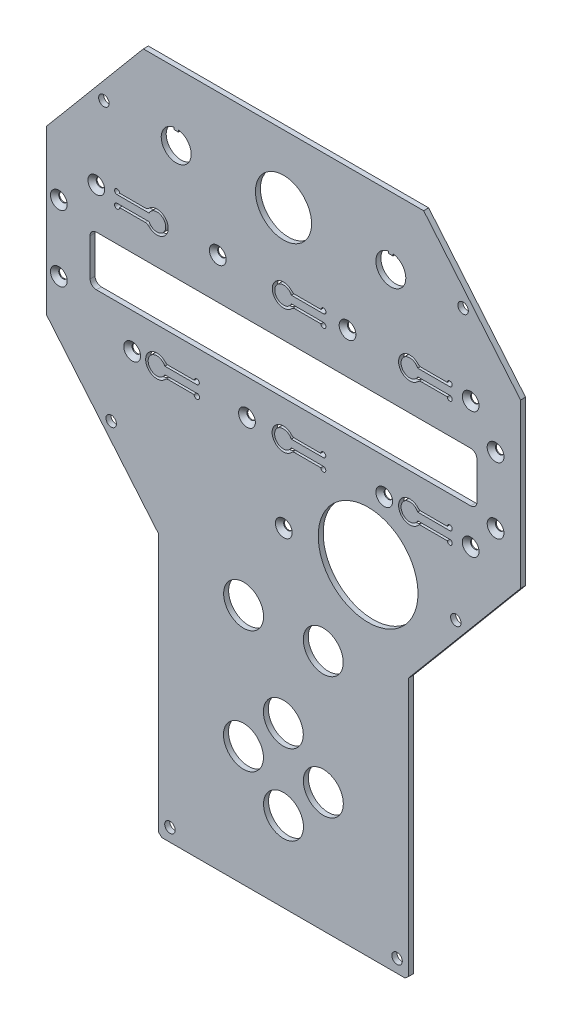
SolidWorks part; units mm, degrees
ref_plane "Plano frontal" through (0, 0, 0) normal (0, 0, 1) x (1, 0, 0)
ref_plane "Plano superior" through (0, 0, 0) normal (0, 1, 0) x (1, 0, 0)
ref_plane "Plano direito" through (0, 0, 0) normal (1, 0, 0) x (0, 0, -1)
sketch "Esboço1" plane through (0, 0, 0) normal (0, 0, 1) x (1, 0, 0)
  line L6 (55.321, 133.8096) -> (-57.007, 133.8096)
  line L7 (-57.007, 133.8096) -> (-95.843, 87.5267)
  line L8 (-95.843, 87.5267) -> (-95.843, 22.1402)
  line L9 (-95.843, 22.1402) -> (-50.843, -31.4887)
  line L10 (-50.843, -31.4887) -> (-50.843, -135.0827)
  line L11 (-50.843, -135.0827) -> (-49.5229, -136.1904)
  line L12 (-49.5229, -136.1904) -> (47.8369, -136.1904)
  line L13 (49.157, -135.0827) -> (47.8369, -136.1904)
  line L14 (49.157, -31.4887) -> (49.157, -135.0827)
  line L15 (94.157, 22.1402) -> (49.157, -31.4887)
  line L16 (94.157, 87.5267) -> (94.157, 22.1402)
  line L17 (55.321, 133.8096) -> (94.157, 87.5267)
  point P16 (-0.843, -136.1904)
  point P17 (-0.843, 133.8096)
extrude "Ressalto-extrusão1" add sketch "Esboço1" along normal blind 2
sketch "Esboço2" plane through (0, 0, 2) normal (0, 0, 1) x (1, 0, 0)
  line L0 (-0.843, -146.6722) -> (-0.843, 180.0647) construction
  line L1 (-95.843, 87.5267) -> (-95.843, 22.1402) construction
  line L2 (55.321, 133.8096) -> (-57.007, 133.8096) construction
  line L3 (-95.843, 22.1402) -> (-50.843, -31.4887) construction
  line L6 (49.157, -135.0827) -> (49.157, -31.4887) construction
  line L7 (-49.5229, -136.1904) -> (47.8369, -136.1904) construction
  line L9 (-50.843, -31.4887) -> (-50.843, -135.0827) construction
  circle A0 centre (-72.8144, 107.9499) radius 2.1
  circle A1 centre (-46.343, -130.9644) radius 2.1
  circle A2 centre (44.657, -130.9644) radius 2.1
  circle A3 centre (71.1284, 107.9499) radius 2.1
  circle A4 centre (-69.8958, -1.7817) radius 2.1
  circle A5 centre (68.2098, -1.7817) radius 2.1
  dimension "D1" = 23.0286
  dimension "D2" = 4.5
  dimension "D3" = 4.5
  dimension "D7" = 25.8597
  dimension "D4" = 5.226
  dimension "D11" = 4.5
extrude "Corte-extrusão1" cut sketch "Esboço2" against normal up to next
sketch "Esboço3" plane through (0, 0, 2) normal (0, 0, 1) x (1, 0, 0)
  line L0 (-95.843, 87.5267) -> (-95.843, 22.1402) construction
  line L1 (-49.5229, -136.1904) -> (47.8369, -136.1904) construction
  line L2 (-75.843, 40.8096) -> (74.157, 40.8096)
  line L3 (-78.343, 43.3096) -> (-78.343, 58.3096)
  line L4 (-75.843, 60.8096) -> (74.157, 60.8096)
  line L5 (76.657, 43.3096) -> (76.657, 58.3096)
  line L6 (-78.343, 40.8096) -> (76.657, 60.8096) construction
  line L7 (-78.343, 60.8096) -> (76.657, 40.8096) construction
  arc A0 (74.157, 60.8096) -> (76.657, 58.3096) centre (74.157, 58.3096) cw
  arc A1 (74.157, 40.8096) -> (76.657, 43.3096) centre (74.157, 43.3096) ccw
  arc A2 (-75.843, 40.8096) -> (-78.343, 43.3096) centre (-75.843, 43.3096) cw
  arc A3 (-78.343, 58.3096) -> (-75.843, 60.8096) centre (-75.843, 58.3096) cw
  dimension "D1" = 2.5
  dimension "D2" = 155
  dimension "D3" = 20
  dimension "D4" = 17.5
  dimension "D5" = 177
extrude "Corte-extrusão2" cut sketch "Esboço3" against normal up to next
sketch "Esboço4" plane through (0, 0, 2) normal (0, 0, 1) x (1, 0, 0)
  line L2 (-49.5229, -136.1904) -> (47.8369, -136.1904) construction
  line L3 (94.157, 22.1402) -> (94.157, 87.5267) construction
  circle A0 centre (33.0563, -0.1904) radius 20
  dimension "D1" = 136
  dimension "D2" = 61.1007
extrude "Corte-extrusão3" cut sketch "Esboço4" against normal up to next
sketch "Esboço5" plane through (0, 0, 2) normal (0, 0, 1) x (1, 0, 0)
  line L2 (55.321, 133.8096) -> (-57.007, 133.8096) construction
  line L3 (-44.743, 112.7417) -> (-44.743, 111.9417)
  line L4 (-44.743, 111.9417) -> (-42.943, 111.9417)
  line L5 (-42.943, 111.9417) -> (-42.943, 112.7417)
  line L6 (41.257, 112.7417) -> (41.257, 111.9417)
  line L7 (41.257, 111.9417) -> (43.057, 111.9417)
  line L8 (43.057, 111.9417) -> (43.057, 112.7417)
  circle A0 centre (-16.8949, -88.1059) radius 8
  circle A1 centre (15.1229, -88.1059) radius 8
  circle A2 centre (-0.843, -104.1412) radius 8
  circle A3 centre (-0.9097, -72.1234) radius 8
  circle A4 centre (-16.8357, -39.1393) radius 8
  circle A5 centre (15.0819, -39.1108) radius 8
  circle A6 centre (-0.843, 106.8096) radius 11.25
  arc A7 (-44.743, 112.7417) -> (-42.943, 112.7417) centre (-43.843, 106.8096) ccw
  arc A8 (41.257, 112.7417) -> (43.057, 112.7417) centre (42.157, 106.8096) ccw
  dimension "D11" = 27
  dimension "D12" = 43
  dimension "D13" = 43
  dimension "D14" = 22.5
  dimension "D15" = 12
  dimension "D16" = 12
  dimension "D18" = 1.8
  dimension "D19" = 0.9
  dimension "D20" = 0.8
  dimension "D21" = 1.8
  dimension "D22" = 0.9
  dimension "D23" = 0.8
extrude "Corte-extrusão4" cut sketch "Esboço5" against normal up to next
sketch "Esboço10" plane through (0, 0, 2) normal (0, 0, 1) x (1, 0, 0)
  line L3 (94.157, 22.1402) -> (94.157, 87.5267) construction
  line L4 (74.157, 60.8096) -> (-75.843, 60.8096) construction
  circle A0 centre (-61.4827, 26.6206) radius 1.75
  circle A1 centre (-15.4827, 26.6206) radius 1.75
  circle A2 centre (39.5173, 26.6206) radius 1.75
  circle A3 centre (84.131, 37.971) radius 1.6
  circle A4 centre (84.131, 64.471) radius 1.6
  circle A5 centre (-90.869, 64.471) radius 1.6
  circle A6 centre (-90.869, 37.971) radius 1.6
  circle A7 centre (-27.183, 77.1996) radius 1.75
  circle A8 centre (24.817, 77.1996) radius 1.75
  circle A9 centre (-0.7327, -4.3294) radius 2
  dimension "D1" = 69.3401
  dimension "D2" = 16.39
  dimension "D3" = 52
  dimension "D4" = 30.95
  dimension "D5" = 14.75
hole_wizard "Escareado para parafuso Allen sextavado escareado de M32" positions "3DSketch3" profile "Esboço11" countersink size "M3" standard "ISO" end condition through all
sketch3d "3DSketch3"
  point P0 (-90.869, 64.471, 2)
  point P3 (-90.869, 37.971, 2)
  point P6 (-61.4827, 26.6206, 2)
  point P9 (-15.4827, 26.6206, 2)
  point P12 (39.5173, 26.6206, 2)
  point P15 (84.131, 37.971, 2)
  point P18 (84.131, 64.471, 2)
  point P21 (24.817, 77.1996, 2)
  point P24 (-27.183, 77.1996, 2)
  point P32 (-0.7327, -4.3294, 2)
sketch "Esboço11" plane through (-90.869, 64.471, 2) normal (1, 0, 0) x (0, -1, 0)
  line L0 (0, 0) -> (0, 2)
  line L1 (0, 2) -> (1.7, 2)
  line L2 (1.7, 2) -> (1.7, 1.66)
  line L3 (1.7, 1.66) -> (3.36, 0)
  line L5 (3.36, 0) -> (0, 0)
  line L6 (-1.7, 1.66) -> (-3.36, 0) construction
  line L11 (0, -6.35) -> (0, 107.95) construction
  dimension "Thru Hole Dia." = 3.4
  dimension "Thru Hole Depth" = 2
  dimension "Near C'Sink Dia." = 6.72
  dimension "Near C'Sink Angle" = 90
sketch "Esboço12" plane through (0, 0, 2) normal (0, 0, 1) x (1, 0, 0)
  line L0 (-75.843, 40.8096) -> (74.157, 40.8096) construction
  line L1 (74.157, 60.8096) -> (-75.843, 60.8096) construction
  line L2 (94.157, 22.1402) -> (94.157, 87.5267) construction
  line L3 (52.9293, 28.0196) -> (65.767, 28.0196)
  line L5 (64.767, 29.0196) -> (53.5087, 29.0196)
  line L6 (52.9293, 25.0196) -> (65.767, 25.0196)
  line L7 (2.2593, 28.0196) -> (15.097, 28.0196)
  line L8 (64.767, 24.0196) -> (53.5087, 24.0196)
  line L9 (14.097, 24.0196) -> (2.8387, 24.0196)
  line L10 (14.097, 29.0196) -> (2.8387, 29.0196)
  line L11 (2.2593, 25.0196) -> (15.097, 25.0196)
  line L12 (-48.4107, 28.0196) -> (-35.573, 28.0196)
  line L13 (-36.6534, 24.0196) -> (-47.8313, 24.0196)
  line L14 (-36.573, 29.0196) -> (-47.8313, 29.0196)
  line L15 (-48.4107, 25.0196) -> (-35.9821, 25.0196)
  line L25 (2.3293, 77.9796) -> (15.167, 77.9796)
  line L26 (52.9293, 77.9796) -> (65.767, 77.9796)
  line L27 (14.167, 78.9796) -> (2.9087, 78.9796)
  line L28 (2.3293, 74.9796) -> (15.167, 74.9796)
  line L29 (-54.6953, 77.9796) -> (-67.533, 77.9796)
  line L30 (14.167, 73.9796) -> (2.9087, 73.9796)
  line L31 (64.767, 78.9796) -> (53.5087, 78.9796)
  line L32 (52.9293, 74.9796) -> (65.767, 74.9796)
  line L34 (64.767, 73.9796) -> (53.5087, 73.9796)
  line L35 (-66.533, 78.9796) -> (-55.2746, 78.9796)
  line L36 (-54.6953, 74.9796) -> (-67.533, 74.9796)
  line L38 (-66.533, 73.9796) -> (-55.2746, 73.9796)
  arc A0 (53.5087, 29.0196) -> (53.5087, 24.0196) centre (49.767, 26.5196) ccw
  arc A2 (15.097, 25.0196) -> (14.097, 24.0196) centre (15.097, 24.0196) cw
  arc A3 (-47.8313, 29.0196) -> (-47.8313, 24.0196) centre (-51.573, 26.5196) ccw
  arc A4 (-55.2746, 73.9796) -> (-55.2746, 78.9796) centre (-51.533, 76.4796) ccw
  arc A5 (2.9087, 78.9796) -> (2.9087, 73.9796) centre (-0.833, 76.4796) ccw
  arc A6 (53.5087, 78.9796) -> (53.5087, 73.9796) centre (49.767, 76.4796) ccw
  arc A7 (52.9293, 28.0196) -> (52.9293, 25.0196) centre (49.767, 26.5196) ccw
  arc A8 (65.767, 28.0196) -> (64.767, 29.0196) centre (65.767, 29.0196) ccw
  arc A9 (64.767, 24.0196) -> (65.767, 25.0196) centre (65.767, 24.0196) ccw
  arc A10 (15.097, 28.0196) -> (14.097, 29.0196) centre (15.097, 29.0196) ccw
  arc A11 (2.8387, 29.0196) -> (2.8387, 24.0196) centre (-0.903, 26.5196) ccw
  arc A12 (2.2593, 28.0196) -> (2.2593, 25.0196) centre (-0.903, 26.5196) ccw
  arc A13 (-35.573, 28.0196) -> (-36.573, 29.0196) centre (-35.573, 29.0196) ccw
  arc A14 (-35.9821, 25.0196) -> (-36.6534, 24.0196) centre (-35.573, 24.0196) cw
  arc A17 (-48.4107, 28.0196) -> (-48.4107, 25.0196) centre (-51.573, 26.5196) ccw
  arc A22 (15.167, 77.9796) -> (14.167, 78.9796) centre (15.167, 78.9796) ccw
  arc A23 (52.9293, 77.9796) -> (52.9293, 74.9796) centre (49.767, 76.4796) ccw
  arc A24 (2.3293, 77.9796) -> (2.3293, 74.9796) centre (-0.833, 76.4796) ccw
  arc A25 (14.167, 73.9796) -> (15.167, 74.9796) centre (15.167, 73.9796) ccw
  arc A26 (65.767, 77.9796) -> (64.767, 78.9796) centre (65.767, 78.9796) ccw
  arc A27 (64.767, 73.9796) -> (65.767, 74.9796) centre (65.767, 73.9796) ccw
  arc A28 (-54.6953, 74.9796) -> (-54.6953, 77.9796) centre (-51.533, 76.4796) ccw
  arc A29 (-66.533, 78.9796) -> (-67.533, 77.9796) centre (-67.533, 78.9796) ccw
  arc A30 (-67.533, 74.9796) -> (-66.533, 73.9796) centre (-67.533, 73.9796) ccw
  dimension "D2" = 14.29
  dimension "D5" = 15.67
  dimension "D6" = 44.39
  dimension "D7" = 50.6
  dimension "D8" = 50.7
  dimension "D9" = 1
  dimension "D13" = 16
  dimension "D14" = 4.5
  dimension "D15" = 3.5
  dimension "D16" = 3.5
  dimension "D17" = 4.5
  dimension "D10" = 1
  dimension "D18" = 16
  dimension "D22" = 3.5
  dimension "D19" = 44.39
  dimension "D33" = 4.5
  dimension "D38" = 4.5
  dimension "D42" = 1
  dimension "D39" = 3.5
  dimension "D44" = 16
  dimension "D46" = 4.5
  dimension "D47" = 3.5
  dimension "D45" = 16
  dimension "D50" = 4.5
  dimension "D51" = 3.5
  dimension "D52" = 16
  dimension "D21" = 50.67
  dimension "D11" = 3
  dimension "D12" = 1.5
  dimension "D20" = 50.67
  dimension "D23" = 16
  dimension "D40" = 3
  dimension "D41" = 1.5
  dimension "D43" = 1
extrude "Corte-extrusão5" cut sketch "Esboço12" against normal blind 10
fillet "Filete1" radius 2 11 edges at (-47.8313, 24.0196, 1) (2.8387, 24.0196, 1) (53.5087, 73.9796, 1) (-47.8313, 29.0196, 1) (2.8387, 29.0196, 1) (53.5087, 29.0196, 1) (53.5087, 78.9796, 1) (2.9087, 73.9796, 1) (2.9087, 78.9796, 1) (-55.2746, 73.9796, 1) (-55.2746, 78.9796, 1)
sketch "Esboço13" plane through (0, 0, 2) normal (0, 0, 1) x (1, 0, 0)
  line L0 (74.157, 60.8096) -> (-75.843, 60.8096) construction
  line L1 (-95.843, 87.5267) -> (-95.843, 22.1402) construction
  line L2 (94.157, 22.1402) -> (94.157, 87.5267) construction
  circle A0 centre (-75.843, 77.1996) radius 2
  circle A1 centre (74.157, 77.1996) radius 2
  circle A9 centre (74.157, 26.6206) radius 2
  circle A10 centre (39.5173, 26.6206) radius 1.7 construction
  dimension "D1" = 16.39
  dimension "D3" = 20
  dimension "D4" = 0
  dimension "D5" = 20
  dimension "D2" = 20
hole_wizard "Escareado para parafuso Allen sextavado escareado de M33" positions "3DSketch4" profile "Esboço14" countersink size "M3" standard "ISO" end condition through all
sketch3d "3DSketch4"
  point P0 (-75.843, 77.1996, 2)
  point P3 (74.157, 77.1996, 2)
  point P6 (74.157, 26.6206, 2)
sketch "Esboço14" plane through (-75.843, 77.1996, 2) normal (1, 0, 0) x (0, -1, 0)
  line L0 (0, 0) -> (0, 2)
  line L1 (0, 2) -> (1.7, 2)
  line L2 (1.7, 2) -> (1.7, 1.66)
  line L3 (1.7, 1.66) -> (3.36, 0)
  line L5 (3.36, 0) -> (0, 0)
  line L6 (-1.7, 1.66) -> (-3.36, 0) construction
  line L11 (0, -6.35) -> (0, 107.95) construction
  dimension "Thru Hole Dia." = 3.4
  dimension "Thru Hole Depth" = 2
  dimension "Near C'Sink Dia." = 6.72
  dimension "Near C'Sink Angle" = 90
